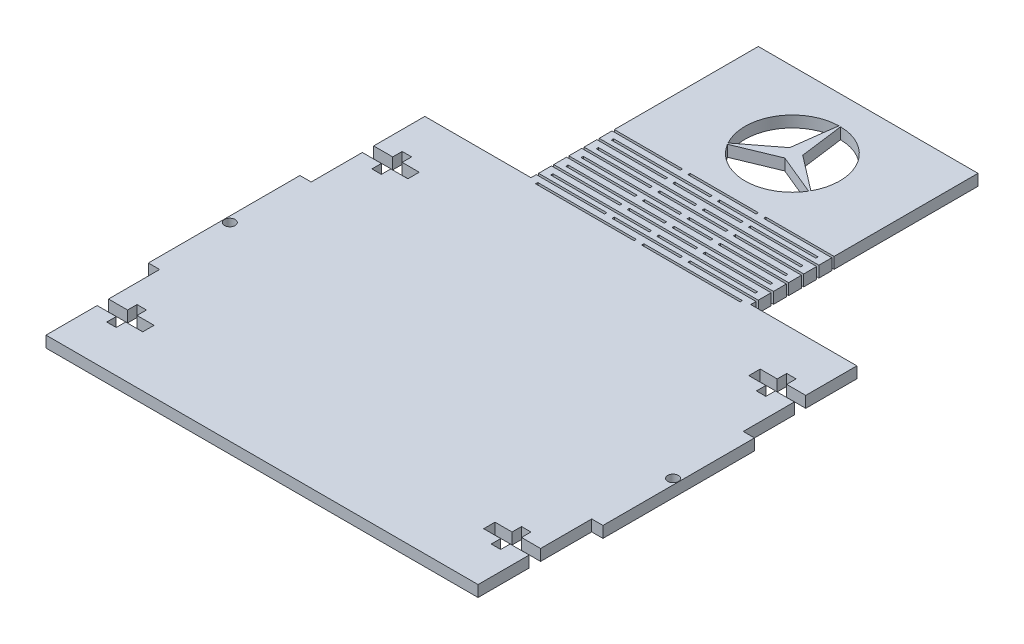
SolidWorks part; units mm, degrees
ref_plane "Front" through (0, 0, 0) normal (0, 0, 1) x (1, 0, 0)
ref_plane "Top" through (0, 0, 0) normal (0, 1, 0) x (1, 0, 0)
ref_plane "Right" through (0, 0, 0) normal (1, 0, 0) x (0, 0, -1)
sketch "草图1" plane through (0, 0, 0) normal (0, 1, 0) x (1, 0, 0)
  line L1 (60, -80) -> (-60, -80)
  line L2 (60, -80) -> (60, 80)
  line L3 (60, 80) -> (-60, 80)
  line L4 (-60, -80) -> (-60, 80)
  line L5 (60, -80) -> (-60, 80) construction
  line L6 (60, 80) -> (-60, -80) construction
  line L7 (-57.0282, 70) -> (-60, 70)
  line L8 (-57.0282, 63.4783) -> (-60, 63.4783)
  line L9 (-57.0282, 56.9565) -> (-60, 56.9565)
  line L10 (-57.0282, 50.4348) -> (-60, 50.4348)
  line L11 (-57.0282, 43.913) -> (-60, 43.913)
  line L12 (-57.0282, 37.3913) -> (-60, 37.3913)
  line L13 (-57.0282, 30.8696) -> (-60, 30.8696)
  line L14 (-57.0282, 24.3478) -> (-60, 24.3478)
  line L15 (-57.0282, 17.8261) -> (-60, 17.8261)
  line L16 (-57.0282, 11.3043) -> (-60, 11.3043)
  line L17 (-57.0282, 4.7826) -> (-60, 4.7826)
  line L18 (-57.0282, -1.7391) -> (-60, -1.7391)
  line L19 (-57.0282, -8.2609) -> (-60, -8.2609)
  line L20 (-57.0282, -14.7826) -> (-60, -14.7826)
  line L21 (-57.0282, -21.3043) -> (-60, -21.3043)
  line L22 (-57.0282, -27.8261) -> (-60, -27.8261)
  line L23 (-57.0282, -34.3478) -> (-60, -34.3478)
  line L24 (-57.0282, -40.8696) -> (-60, -40.8696)
  line L25 (-57.0282, -47.3913) -> (-60, -47.3913)
  line L26 (-57.0282, -53.913) -> (-60, -53.913)
  line L27 (-57.0282, -60.4348) -> (-60, -60.4348)
  line L28 (-57.0282, -66.9565) -> (-60, -66.9565)
  line L29 (-57.0282, -73.4783) -> (-60, -73.4783)
  line L30 (-57.0282, -80) -> (-60, -80)
  line L31 (0, 0) -> (0, 80)
  line L32 (0, 0) -> (0, -80)
  line L33 (-57.0282, -93.0435) -> (-60, -93.0435) [skipped]
  line L34 (-57.0282, -86.5217) -> (-60, -86.5217) [skipped]
  point P0 (0, 0)
  dimension "D1" = 120
  dimension "D2" = 160
  dimension "D4" = 10
  dimension "D5" = 26
extrude "凸台-拉伸1" add sketch "草图1" along normal blind 2.9718
ref_plane "基准面1" through (-60, 2.9718, -80) normal (-1, 0, 0) x (0, 0, 1)
sketch "草图3" plane through (0, 2.9718, 0) normal (0, 1, 0) x (1, 0, 0)
  line L0 (-29, 80) -> (-29, 20)
  line L1 (60, 80) -> (-60, 80) construction
  line L2 (-29, 20) -> (-30, 20)
  line L3 (-30, 20) -> (-30, 80)
  line L4 (-29, 80) -> (-30, 80)
  dimension "D1" = 60
  dimension "D2" = 30
  dimension "D3" = 1
extrude "切除-拉伸1" cut sketch "草图3" against normal blind 26
sketch "草图5" plane through (0, 2.9718, 0) normal (0, 1, 0) x (1, 0, 0)
  line L1 (-29, 30) -> (-11, 30)
  line L2 (-29, 30) -> (-29, 29.4)
  line L3 (-29, 29.4) -> (-11, 29.4)
  line L4 (-11, 30) -> (-11, 29.4)
  line L6 (60, 80) -> (-29, 80) construction
  line L7 (-29, 20) -> (-29, 80) construction
  dimension "D1" = 18
  dimension "D2" = 50
  dimension "D3" = 0.6
  dimension "D4" = 0
extrude "切除-拉伸2" cut sketch "草图5" against normal blind 26 contours L1 L4 L3 L2
pattern_linear "阵列(线性)1" count 4 spacing 4 along (0, 0, -1) count 3 spacing 4 along (0, 0, 1) of "切除-拉伸2"
mirror "镜向2" about plane through (0, 0, 0) normal (1, 0, 0) of "切除-拉伸1", "阵列(线性)1", "切除-拉伸2"
sketch "草图7" plane through (0, 2.9718, 0) normal (0, 1, 0) x (1, 0, 0)
  line L0 (-9, 42) -> (9, 42)
  line L1 (-9, 41.4) -> (9, 41.4)
  line L2 (-29, 41.4) -> (-11, 41.4) construction
  line L3 (-9, 42) -> (-9, 41.4)
  line L4 (9, 42) -> (9, 41.4)
  line L5 (-11, 42) -> (-11, 41.4) construction
  dimension "D1" = 18
  dimension "D2" = 2
  dimension "D3" = 0.6
  dimension "D4" = 0.6
extrude "切除-拉伸3" cut sketch "草图7" against normal blind 26
pattern_linear "阵列(线性)2" count 6 spacing 4 along (0, 0, 1) of "切除-拉伸3"
sketch "草图8" plane through (0, 2.9718, 0) normal (0, 1, 0) x (1, 0, 0)
  line L0 (29, 38) -> (29, 41.4) construction
  line L1 (-27, 39.8) -> (-1, 39.8)
  line L2 (-27, 39.8) -> (-27, 39.2)
  line L3 (-27, 39.2) -> (-1, 39.2)
  line L4 (-1, 39.8) -> (-1, 39.2)
  line L5 (1, 39.8) -> (27, 39.8)
  line L6 (1, 39.8) -> (1, 39.2)
  line L7 (1, 39.2) -> (27, 39.2)
  line L8 (27, 39.8) -> (27, 39.2)
  line L9 (29, 38) -> (11, 38) construction
  line L10 (-29, 38) -> (-11, 38) construction
  line L11 (-29, 38) -> (-29, 41.4) construction
  dimension "D1" = 26
  dimension "D2" = 0.6
  dimension "D3" = 0.6
  dimension "D4" = 26
  dimension "D5" = 2
  dimension "D6" = 1.2
  dimension "D7" = 1.2
  dimension "D8" = 2
extrude "切除-拉伸4" cut sketch "草图8" against normal blind 26
pattern_linear "阵列(线性)3" count 6 spacing 4 along (0, 0, 1) of "切除-拉伸4"
sketch "草图9" plane through (0, 2.9718, 0) normal (0, 1, 0) x (1, 0, 0)
  line L0 (29, 80) -> (-29, 80) construction
  line L1 (0, 60) -> (-1.7321, 61)
  line L2 (-1.7321, 61) -> (1.7321, 61)
  line L3 (1.7321, 61) -> (0, 60)
  line L4 (0, 60) -> (1.7321, 61)
  line L5 (-1.7321, 61) -> (0, 58)
  line L6 (0, 58) -> (1.7321, 61)
  line L7 (0, 60) -> (0, 58)
  line L8 (-1.7321, 61) -> (-0.2183, 72.4981)
  line L9 (1.7321, 61) -> (0.2183, 72.4981)
  line L10 (1.7321, 61) -> (10.9328, 53.94)
  line L11 (0, 58) -> (10.7145, 53.5619)
  line L12 (0, 58) -> (-10.7145, 53.5619)
  line L13 (-1.7321, 61) -> (-10.9328, 53.94)
  circle A0 centre (0, 60) radius 12.5
  point P20 (0, 60)
  dimension "D1" = 25
  dimension "D2" = 20
  dimension "D3" = 120
  dimension "D4" = 120
  dimension "D5" = 2
  dimension "D6" = 2
  dimension "D7" = 97.5
  dimension "D8" = 82.5
  dimension "D9" = 3
extrude "切除-拉伸5" cut sketch "草图9" against normal blind 26 contours L8 A0 L13 | L10 A0 L9 | L12 A0 L11
sketch "草图10" plane through (0, 2.9718, 0) normal (0, 1, 0) x (1, 0, 0)
  line L1 (-30, 80) -> (-70, 80)
  line L2 (-30, 80) -> (-30, 20)
  line L3 (-30, 20) -> (-70, 20)
  line L4 (-70, 80) -> (-70, 20)
  dimension "D1" = 60
  dimension "D2" = 40
extrude "切除-拉伸6" cut sketch "草图10" against normal blind 10
mirror "镜向3" about plane through (0, 0, 0) normal (1, 0, 0) of "切除-拉伸6"
sketch "草图11" plane through (0, 2.9718, 0) normal (0, 1, 0) x (1, 0, 0)
  line L0 (-57.0282, 20) -> (-57.0282, -10)
  line L1 (-60, 20) -> (-29, 20) construction
  line L2 (-57.0282, -10) -> (-60, -10)
  line L3 (-60, -80) -> (-60, 20) construction
  line L4 (-60, -10) -> (-60, 20)
  line L5 (-60, 20) -> (-57.0282, 20)
  line L7 (-60, -80) -> (-57.0282, -80)
  line L8 (-60, -80) -> (-60, -50)
  line L9 (-60, -50) -> (-57.0282, -50)
  line L10 (-57.0282, -80) -> (-57.0282, -50)
  dimension "D1" = 2.9718
  dimension "D2" = 2.9718
  dimension "D3" = 30
  dimension "D4" = 30
extrude "切除-拉伸7" cut sketch "草图11" against normal blind 10
mirror "镜向4" about plane through (0, 0, 0) normal (1, 0, 0) of "切除-拉伸7"
sketch "草图12" plane through (0, 2.9718, 0) normal (0, 1, 0) x (1, 0, 0)
  line L0 (-60, -50) -> (-60, -10) construction
  line L1 (-57.0282, -50) -> (-60, -50) construction
  circle A0 centre (-58.5, -30) radius 1.4
  dimension "D1" = 1.5
  dimension "D2" = 2.8
  dimension "D3" = 20
extrude "切除-拉伸8" cut sketch "草图12" against normal blind 10
sketch "草图13" plane through (0, 2.9718, 0) normal (0, 1, 0) x (1, 0, 0)
  line L0 (-60, 3.5) -> (-52, 3.5)
  line L1 (-52, 3.5) -> (-52, 1)
  line L2 (-52, 1) -> (-49.5, 1)
  line L3 (-49.5, 1) -> (-49.5, 3.5)
  line L4 (-49.5, 3.5) -> (-45, 3.5)
  line L5 (-45, 3.5) -> (-45, 6.5)
  line L6 (-45, 5) -> (-60, 5)
  line L7 (-60, 6.5) -> (-60, 3.5)
  line L8 (-49.5, 6.5) -> (-45, 6.5)
  line L9 (-52, 9) -> (-49.5, 9)
  line L10 (-49.5, 9) -> (-49.5, 6.5)
  line L11 (-60, 6.5) -> (-52, 6.5)
  line L12 (-52, 6.5) -> (-52, 9)
  line L13 (-60, -50) -> (-60, -10) construction
  line L14 (-57.0282, 20) -> (-29, 20) construction
  point P13 (-52.5, 5)
  dimension "D1" = 1.5
  dimension "D2" = 1.5
  dimension "D3" = 4
  dimension "D4" = 0
  dimension "D5" = 15
  dimension "D6" = 8
  dimension "D7" = 2.5
  dimension "D8" = 15
extrude "切除-拉伸9" cut sketch "草图13" against normal blind 10 contours L12 L11 L7 L6 L5 L8 L10 L9 | L6 L7 L0 L1 L2 L3 L4 L5
pattern_linear "阵列(线性)4" count 2 spacing 70 along (0, 0, 1) of "切除-拉伸9"
mirror "镜向5" about plane through (0, 0, 0) normal (1, 0, 0) of "阵列(线性)4", "切除-拉伸9"
mirror "镜向6" about plane through (0, 0, 0) normal (1, 0, 0) of "切除-拉伸8"
